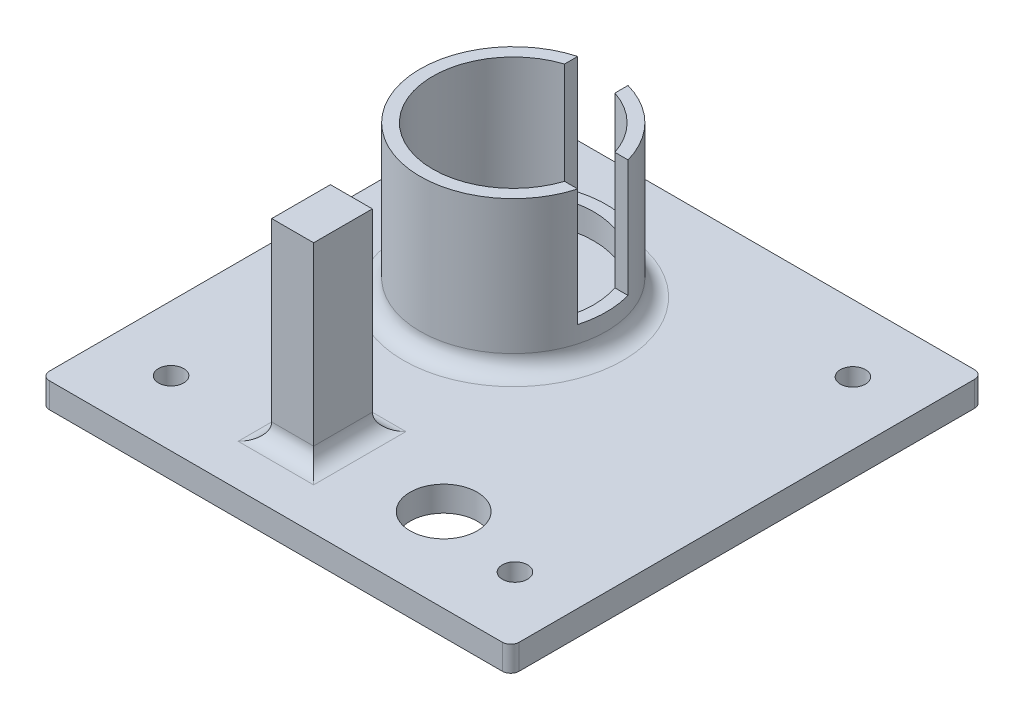
SolidWorks part; units mm, degrees
ref_plane "Front Plane" through (0, 0, 0) normal (0, 0, 1) x (1, 0, 0)
ref_plane "Top Plane" through (0, 0, 0) normal (0, 1, 0) x (1, 0, 0)
ref_plane "Right Plane" through (0, 0, 0) normal (1, 0, 0) x (0, 0, -1)
sketch "Sketch1" plane through (0, 5.441, 0) normal (0, 1, 0) x (-0.5023, 0, -0.8647)
  line L0 (-182.04, -110.7697) -> (-135.0871, -138.0445) construction
  line L1 (-133.7202, -137.6821) -> (-106.596, -90.9887) construction
  line L2 (-106.9584, -89.6217) -> (-153.9113, -62.3468) construction
  line L3 (-155.2783, -62.7092) -> (-182.4024, -109.4027) construction
  line L4 (-182.04, -110.7697) -> (-135.0871, -138.0445)
  line L5 (-133.7202, -137.6821) -> (-106.596, -90.9887)
  line L6 (-106.9584, -89.6217) -> (-153.9113, -62.3468)
  line L7 (-155.2783, -62.7092) -> (-182.4024, -109.4027)
  arc A0 (-135.0871, -138.0445) -> (-133.7202, -137.6821) centre (-134.5848, -137.1798) ccw construction
  arc A1 (-106.596, -90.9887) -> (-106.9584, -89.6217) centre (-107.4607, -90.4864) ccw construction
  arc A2 (-153.9113, -62.3468) -> (-155.2783, -62.7092) centre (-154.4136, -63.2115) ccw construction
  arc A3 (-182.4024, -109.4027) -> (-182.04, -110.7697) centre (-181.5377, -109.905) ccw construction
  arc A4 (-135.0871, -138.0445) -> (-133.7202, -137.6821) centre (-134.5848, -137.1798) ccw
  arc A5 (-106.596, -90.9887) -> (-106.9584, -89.6217) centre (-107.4607, -90.4864) ccw
  arc A6 (-153.9113, -62.3468) -> (-155.2783, -62.7092) centre (-154.4136, -63.2115) ccw
  arc A7 (-182.4024, -109.4027) -> (-182.04, -110.7697) centre (-181.5377, -109.905) ccw
extrude "Boss-Extrude1" add sketch "Sketch1" along normal blind 3
sketch "Sketch2" plane through (0, 8.441, 0) normal (0, 1, 0) x (1, 0, 0)
  line L0 (131.2204, -47.4694) -> (131.2204, -101.7694) construction
  line L1 (186.2204, -46.4694) -> (132.2204, -46.4694) construction
  circle A0 centre (151.2204, -66.4694) radius 11.1
  dimension "D1" = 22.2
  dimension "D2" = 20
  dimension "D3" = 20
extrude "Boss-Extrude2" add sketch "Sketch2" along normal blind 18
sketch "Sketch3" plane through (0, 26.441, 0) normal (0, 1, 0) x (1, 0, 0)
  circle A0 centre (151.2204, -66.4694) radius 9.6
  dimension "D1" = 19.2
extrude "Cut-Extrude1" cut sketch "Sketch3" against normal blind 17
fillet "Fillet1" radius 2 1 edges at (151.2204, 8.441, 77.5694)
sketch "Sketch4" plane through (0, 26.441, 0) normal (0, 1, 0) x (1, 0, 0)
  line L1 (166.2204, -69.4694) -> (156.2204, -69.4694)
  line L2 (166.2204, -69.4694) -> (166.2204, -63.4694)
  line L3 (166.2204, -63.4694) -> (156.2204, -63.4694)
  line L4 (156.2204, -69.4694) -> (156.2204, -63.4694)
  line L5 (154.2204, -70.4694) -> (148.2204, -70.4694)
  line L6 (154.2204, -70.4694) -> (154.2204, -52.4694)
  line L7 (154.2204, -52.4694) -> (148.2204, -52.4694)
  line L8 (148.2204, -70.4694) -> (148.2204, -52.4694)
  circle A1 centre (151.2204, -66.4694) radius 9.6 construction
  dimension "D1" = 5
  dimension "D2" = 10
  dimension "D3" = 6
  dimension "D4" = 3
  dimension "D5" = 6
  dimension "D6" = 3
  dimension "D7" = 18
  dimension "D8" = 4
extrude "Cut-Extrude2" cut sketch "Sketch4" against normal blind 14
sketch "Sketch5" plane through (0, 8.441, 0) normal (0, 1, 0) x (1, 0, 0)
  line L0 (187.2204, -101.7694) -> (187.2204, -47.4694) construction
  line L1 (132.2204, -102.7694) -> (186.2204, -102.7694) construction
  circle A0 centre (169.2204, -92.7694) radius 4
  dimension "D1" = 8
  dimension "D2" = 18
  dimension "D3" = 10
extrude "Cut-Extrude3" cut sketch "Sketch5" against normal blind 4
sketch "Sketch6" plane through (0, 8.441, 0) normal (0, 1, 0) x (1, 0, 0)
  circle A0 centre (179.7204, -54.4694) radius 1.5
  circle A1 centre (179.7204, -94.7694) radius 1.5
  circle A2 centre (138.9528, -95.0031) radius 1.5
  dimension "D1" = 3
  dimension "D2" = 3
  dimension "D3" = 3
extrude "Cut-Extrude4" cut sketch "Sketch6" against normal up to next
sketch "Sketch7" plane through (0, 8.441, 0) normal (0, 1, 0) x (1, 0, 0)
  line L0 (187.2204, -101.7694) -> (187.2204, -47.4694) construction
  line L1 (156.7204, -88.7694) -> (151.7204, -88.7694)
  line L2 (156.7204, -88.7694) -> (156.7204, -95.7694)
  line L3 (156.7204, -95.7694) -> (151.7204, -95.7694)
  line L4 (151.7204, -88.7694) -> (151.7204, -95.7694)
  line L5 (132.2204, -102.7694) -> (186.2204, -102.7694) construction
  point P4 (0, 0)
  point P7 (0, 0)
  dimension "D1" = 7
  dimension "D2" = 5
  dimension "D3" = 30.5
  dimension "D4" = 7
extrude "Boss-Extrude3" add sketch "Sketch7" along normal blind 23
fillet "Fillet2" radius 2 4 edges at (154.2204, 8.441, 88.7694) (156.7204, 8.441, 92.2694) (154.2204, 8.441, 95.7694) (151.7204, 8.441, 92.2694)
